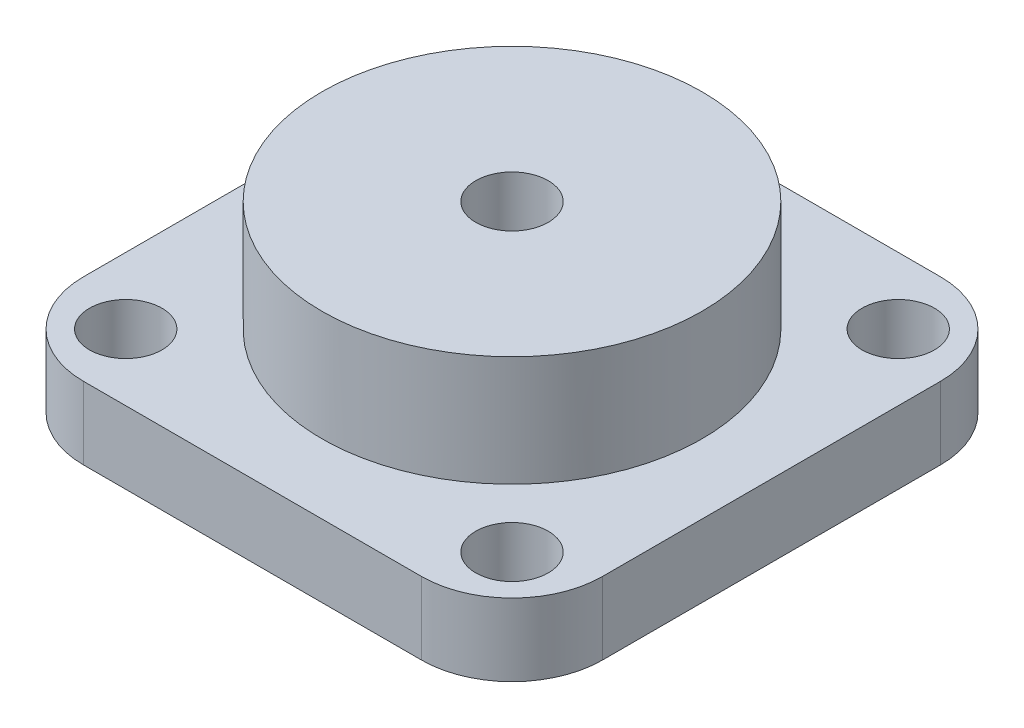
SolidWorks part; units mm, degrees
ref_plane "Front Plane" through (0, 0, 0) normal (0, 0, 1) x (1, 0, 0)
ref_plane "Top Plane" through (0, 0, 0) normal (0, 1, 0) x (1, 0, 0)
ref_plane "Right Plane" through (0, 0, 0) normal (1, 0, 0) x (0, 0, -1)
sketch "Sketch1" plane through (0, 0, 0) normal (0, 1, 0) x (1, 0, 0)
  line L1 (-15, 0) -> (-71, 0)
  line L2 (0, -15) -> (0, -71)
  line L3 (-15, -86) -> (-71, -86)
  line L4 (-86, -15) -> (-86, -71)
  arc A0 (-15, 0) -> (0, -15) centre (-15, -15) cw
  arc A1 (0, -71) -> (-15, -86) centre (-15, -71) cw
  arc A2 (-71, -86) -> (-86, -71) centre (-71, -71) cw
  arc A3 (-71, 0) -> (-86, -15) centre (-71, -15) ccw
  point P7 (0, 0)
  dimension "D3" = 15
  dimension "D1" = 86
  dimension "D2" = 86
extrude "Boss-Extrude1" add sketch "Sketch1" along normal blind 12
sketch "Sketch2" plane through (0, 12, 0) normal (0, 1, 0) x (1, 0, 0)
  line L0 (-75, -11) -> (-11, -11) construction
  line L1 (-11, -11) -> (-11, -75) construction
  line L2 (-11, -75) -> (-75, -75) construction
  line L3 (-75, -75) -> (-75, -11) construction
  line L4 (-75, -11) -> (-75, 0) construction
  line L5 (-15, 0) -> (-71, 0) construction
  line L6 (-75, -11) -> (-86, -11) construction
  line L7 (-86, -15) -> (-86, -71) construction
  line L8 (-11, -11) -> (0, -11) construction
  line L9 (0, -71) -> (0, -15) construction
  line L10 (-11, -11) -> (-11, 0) construction
  line L11 (-11, -75) -> (0, -75) construction
  line L12 (-11, -75) -> (-11, -86) construction
  line L13 (-71, -86) -> (-15, -86) construction
  line L14 (-75, -75) -> (-75, -86) construction
  line L15 (-75, -75) -> (-86, -75) construction
  circle A0 centre (-75, -11) radius 6
  circle A1 centre (-11, -11) radius 6
  circle A2 centre (-11, -75) radius 6
  circle A3 centre (-75, -75) radius 6
  dimension "D3" = 12
  dimension "D1" = 64
  dimension "D2" = 64
extrude "Cut-Extrude1" cut sketch "Sketch2" against normal blind 12
sketch "Sketch3" plane through (0, 12, 0) normal (0, 1, 0) x (1, 0, 0)
  line L0 (-43, 0) -> (-43, -86) construction
  line L1 (-15, 0) -> (-71, 0) construction
  line L2 (-71, -86) -> (-15, -86) construction
  circle A0 centre (-43, -43) radius 31.5
  dimension "D1" = 63
extrude "Boss-Extrude2" add sketch "Sketch3" along normal blind 18.3
sketch "Sketch4" plane through (0, 30.3, 0) normal (0, 1, 0) x (1, 0, 0)
  line L0 (-43, -11.5) -> (-43, -43) construction
  circle A0 centre (-43, -43) radius 31.5 construction
  circle A1 centre (-43, -43) radius 31.5 construction
  circle A2 centre (-43, -43) radius 6
  dimension "D1" = 12
extrude "Cut-Extrude2" cut sketch "Sketch4" against normal through all
